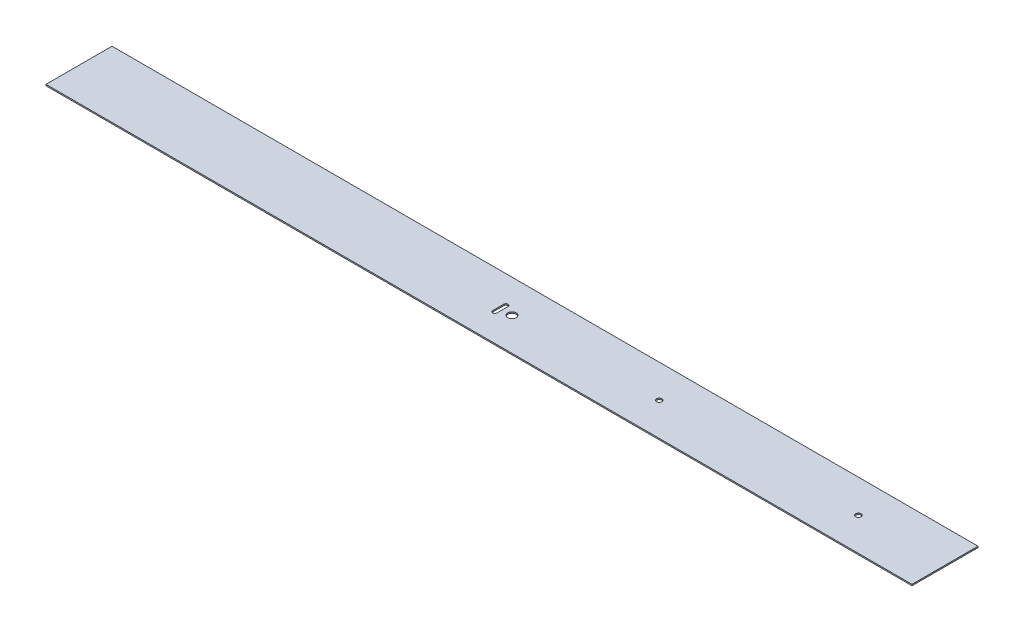
SolidWorks part; units mm, degrees
ref_plane "Front Plane" through (0, 0, 0) normal (0, 0, 1) x (1, 0, 0)
ref_plane "Top Plane" through (0, 0, 0) normal (0, 1, 0) x (1, 0, 0)
ref_plane "Right Plane" through (0, 0, 0) normal (1, 0, 0) x (0, 0, -1)
sketch "Sketch1" plane through (0, 0, 0) normal (0, 1, 0) x (1, 0, 0)
  line L0 (-13.4, -6.35) -> (-13.4, 6.35) construction
  line L1 (-500, 38.1) -> (500, 38.1)
  line L2 (-500, 38.1) -> (-500, -38.1)
  line L3 (-500, -38.1) -> (500, -38.1)
  line L4 (500, 38.1) -> (500, -38.1)
  line L5 (-500, 38.1) -> (500, -38.1) construction
  line L6 (-500, -38.1) -> (500, 38.1) construction
  line L7 (-15.8, -6.35) -> (-15.8, 6.35)
  line L8 (-11, -6.35) -> (-11, 6.35)
  circle A0 centre (0, 0) radius 4.83
  arc A1 (-15.8, -6.35) -> (-11, -6.35) centre (-13.4, -6.35) ccw
  arc A2 (-11, 6.35) -> (-15.8, 6.35) centre (-13.4, 6.35) ccw
  point P0 (0, 0)
  point P10 (-13.4, 0)
  point P15 (-13.4, -8.75)
  point P16 (-13.4, 8.75)
  point P17 (-4.83, 0)
  dimension "D3" = 9.66
  dimension "D1" = 1000
  dimension "D2" = 76.2
  dimension "D4" = 4.8
  dimension "D5" = 17.5
  dimension "D6" = 6.17
extrude "Boss-Extrude1" add sketch "Sketch1" along normal mid plane 1.5
sketch "Sketch2" plane through (0, 0.75, 0) normal (0, 1, 0) x (1, 0, 0)
  circle A0 centre (170, 0) radius 2.98
  circle A1 centre (400, 0) radius 3.11
  point P4 (0, 0)
  point P6 (0, 0)
  dimension "D1" = 5.96
  dimension "D2" = 6.22
  dimension "D3" = 170
  dimension "D4" = 400
extrude "Cut-Extrude1" cut sketch "Sketch2" against normal through all
